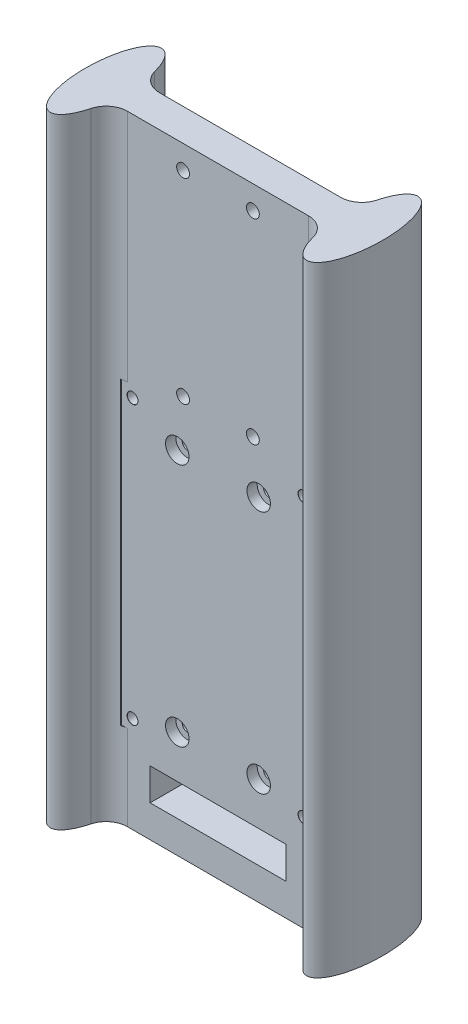
SolidWorks part; units mm, degrees
ref_plane "Front Plane" through (0, 0, 0) normal (0, 0, 1) x (1, 0, 0)
ref_plane "Top Plane" through (0, 0, 0) normal (0, 1, 0) x (1, 0, 0)
ref_plane "Right Plane" through (0, 0, 0) normal (1, 0, 0) x (0, 0, -1)
sketch "Sketch1" plane through (0, 0, 0) normal (0, 1, 0) x (1, 0, 0)
  line L0 (-30, 0) -> (-34.85, 0) construction
  line L1 (30, 3.75) -> (-30, 3.75)
  line L2 (30, 3.75) -> (30, -3.75)
  line L3 (30, -3.75) -> (-30, -3.75)
  line L4 (-30, 3.75) -> (-30, -3.75)
  line L5 (30, 3.75) -> (-30, -3.75) construction
  line L6 (30, -3.75) -> (-30, 3.75) construction
  line L7 (30, 0) -> (34.85, 0) construction
  ellipse E0 centre (-30, 0) end of major axis (-30, -13) minor radius 4.85
  ellipse E1 centre (30, 0) end of major axis (30, 13) minor radius 4.85
  point P0 (0, 0)
  dimension "D1" = 69.7
  dimension "D2" = 7.5
  dimension "D4" = 60
  dimension "D6" = 13
  dimension "D7" = 13
extrude "Boss-Extrude1" add sketch "Sketch1" along normal blind 145 contours E1 L1 E0 L3 | L3 E0 L1 L4 | L1 E0 L3 L4 | L1 E1 L3 L2 | L3 E1 L1 L2
fillet "Fillet1" radius 5 4 edges at (-25.3562, 72.5, -3.75) (25.3562, 72.5, -3.75) (25.3562, 72.5, 3.75) (-25.3562, 72.5, 3.75)
sketch "Sketch3" plane through (0, 0, -3.75) normal (0, 0, -1) x (-1, 0, 0)
  line L0 (0, 61.275) -> (0, 0) construction
  line L1 (15.875, 20) -> (-15.875, 20)
  line L2 (15.875, 20) -> (15.875, 102.55)
  line L3 (15.875, 102.55) -> (-15.875, 102.55)
  line L4 (-15.875, 20) -> (-15.875, 102.55)
  line L5 (15.875, 20) -> (-15.875, 102.55) construction
  line L6 (15.875, 102.55) -> (-15.875, 20) construction
  line L7 (21.1972, 0) -> (26.0334, 0) construction
  line L8 (-21.1972, 0) -> (21.1972, 0) construction
  line L9 (20.875, 102.55) -> (25.875, 102.55)
  line L10 (9.525, 25) -> (-9.525, 25)
  line L11 (9.525, 25) -> (9.525, 82.15)
  line L12 (9.525, 82.15) -> (-9.525, 82.15)
  line L13 (-9.525, 25) -> (-9.525, 82.15)
  line L14 (9.525, 25) -> (-9.525, 82.15) construction
  line L15 (9.525, 82.15) -> (-9.525, 25) construction
  line L16 (20.875, 102.55) -> (20.875, 20)
  line L17 (20.875, 20) -> (25.875, 20)
  line L18 (25.875, 102.55) -> (25.875, 20)
  line L19 (0, 53.575) -> (0, 20) construction
  line L20 (-15.875, 7.5) -> (15.875, 7.5)
  line L21 (-15.875, 7.5) -> (-15.875, 15)
  line L22 (-15.875, 15) -> (15.875, 15)
  line L23 (15.875, 7.5) -> (15.875, 15)
  point P0 (0, 61.275)
  dimension "D1" = 31.75
  dimension "D2" = 82.55
  dimension "D3" = 20
  dimension "D4" = 57.15
  dimension "D5" = 19.05
  dimension "D6" = 5
  dimension "D7" = 5
  dimension "D8" = 82.55
  dimension "D9" = 20
  dimension "D10" = 7.5
  dimension "D11" = 7.5
  dimension "D12" = 5
extrude "Cut-Extrude2" cut sketch "Sketch3" against normal through all both and the other way through all contours L21 L20 L23 L22
hole_wizard "Tap Drill for M3x0.5 Tap1" positions "3DSketch1" profile "Sketch4" hole size "M3x0.5" standard "ANSI Metric" end condition through all
sketch3d "3DSketch1"
  point P0 (9.525, 82.15, -3.75)
  point P3 (-9.525, 82.15, -3.75)
  point P6 (-9.525, 25, -3.75)
  point P9 (9.525, 25, -3.75)
sketch "Sketch4" plane through (9.525, 82.15, -3.75) normal (1, 0, 0) x (0, 1, 0)
  line L0 (0, 0) -> (0, 16.75)
  line L1 (0, 16.75) -> (1.25, 16.75)
  line L2 (1.25, 16.75) -> (1.25, 0)
  line L5 (1.25, 0) -> (0, 0)
  line L11 (0, -6.35) -> (0, 107.95) construction
  dimension "Thru Hole Dia." = 2.5
  dimension "Thru Hole Depth" = 16.75
sketch "Sketch5" plane through (0, 0, 3.75) normal (0, 0, 1) x (1, 0, 0)
  line L0 (-15.875, 15) -> (15.875, 15) construction
  line L1 (17.5, 25) -> (-17.5, 25)
  line L2 (17.5, 25) -> (17.5, 85)
  line L3 (17.5, 85) -> (-17.5, 85)
  line L4 (-17.5, 25) -> (-17.5, 85)
  line L5 (17.5, 25) -> (-17.5, 85) construction
  line L6 (17.5, 85) -> (-17.5, 25) construction
  line L7 (22.6, 19.9) -> (22.6, 90.1)
  line L8 (0, 15) -> (0, 55) construction
  line L9 (22.6, 90.1) -> (-22.6, 90.1)
  line L10 (-22.6, 19.9) -> (-22.6, 90.1)
  line L11 (22.6, 19.9) -> (-22.6, 19.9)
  line L12 (20, 22.5) -> (20, 87.5) construction
  line L13 (20, 87.5) -> (-20, 87.5) construction
  line L14 (-20, 22.5) -> (-20, 87.5) construction
  line L15 (20, 22.5) -> (-20, 22.5) construction
  point P0 (0, 55)
  dimension "D1" = 40
  dimension "D2" = 60
  dimension "D3" = 35
  dimension "D4" = 5.1
  dimension "D5" = 2.5
extrude "Cut-Extrude3" cut sketch "Sketch5" along normal blind 10
sketch "Sketch6" plane through (0, 0, 3.75) normal (0, 0, 1) x (1, 0, 0)
  circle A0 centre (9.525, 82.15) radius 2.75
  circle A1 centre (-9.525, 82.15) radius 2.75
  circle A2 centre (9.525, 25) radius 2.75
  circle A4 centre (-9.525, 25) radius 2.75
  dimension "D1" = 5.5
  dimension "D2" = 5.5
  dimension "D3" = 5.5
  dimension "D4" = 5.5
extrude "Cut-Extrude4" cut sketch "Sketch6" against normal blind 2.4
sketch "Sketch7" plane through (0, 0, 3.75) normal (0, 0, 1) x (1, 0, 0)
  point P0 (-20, 87.5)
  point P3 (20, 87.5)
  point P6 (20, 22.5)
  point P9 (-20, 22.5)
hole_wizard "Tap Drill for M3 Tap1" positions "Sketch7" profile "Sketch8" hole size "M3" standard "ISO" end condition through all
sketch "Sketch8" plane through (-20, 87.5, 3.75) normal (1, 0, 0) x (0, -1, 0)
  line L0 (0, 0) -> (0, 16.75)
  line L1 (0, 16.75) -> (1.25, 16.75)
  line L2 (1.25, 16.75) -> (1.25, 0.025)
  line L3 (1.25, 0.025) -> (1.275, 0)
  line L5 (1.275, 0) -> (0, 0)
  line L6 (-1.25, 0.025) -> (-1.275, 0) construction
  line L11 (0, -6.35) -> (0, 107.95) construction
  dimension "Thru Hole Dia." = 2.5
  dimension "Thru Hole Depth" = 16.75
  dimension "Near C'Sink Dia." = 2.55
  dimension "Near C'Sink Angle" = 90
sketch "Sketch9" plane through (0, 0, -3.75) normal (0, 0, -1) x (-1, 0, 0)
  line L0 (0, 0) -> (0, 145) construction
  line L1 (-21.1972, 0) -> (21.1972, 0) construction
  line L2 (-21.1972, 145) -> (21.1972, 145) construction
  line L3 (0, 116.6) -> (-10.668, 116.6) construction
  line L4 (10.668, 142) -> (-10.668, 142)
  line L5 (10.668, 142) -> (10.668, 91.2)
  line L6 (10.668, 91.2) -> (-10.668, 91.2)
  line L7 (-10.668, 142) -> (-10.668, 91.2)
  line L8 (10.668, 142) -> (-10.668, 91.2) construction
  line L9 (10.668, 91.2) -> (-10.668, 142) construction
  circle A0 centre (-8.168, 139.5) radius 1.5
  circle A1 centre (-8.168, 93.7) radius 1.5
  circle A2 centre (8.168, 93.7) radius 1.5
  circle A3 centre (8.168, 139.5) radius 1.5
  point P6 (0, 116.6)
  dimension "D4" = 3
  dimension "D6" = 2.5
  dimension "D1" = 21.336
  dimension "D2" = 50.8
  dimension "D3" = 3
  dimension "D5" = 2.5
extrude "Cut-Extrude5" cut sketch "Sketch9" against normal through all contours A0 | A3 | A2 | A1
